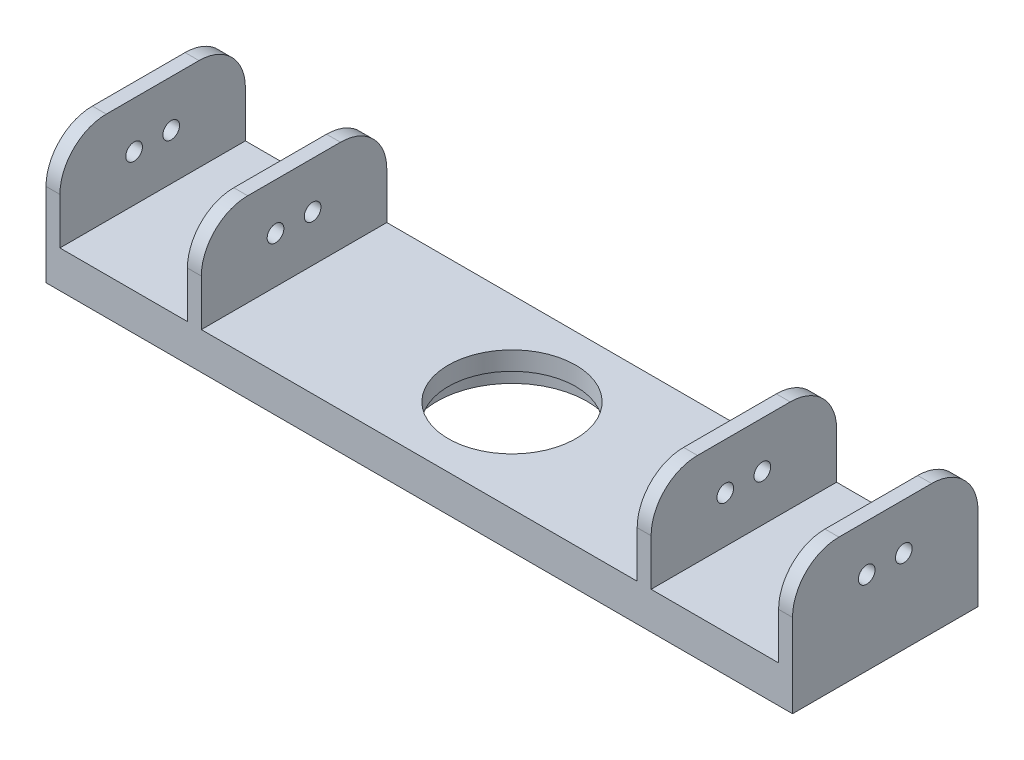
SolidWorks part; units mm, degrees
ref_plane "Front Plane" through (0, 0, 0) normal (0, 0, 1) x (1, 0, 0)
ref_plane "Top Plane" through (0, 0, 0) normal (0, 1, 0) x (1, 0, 0)
ref_plane "Right Plane" through (0, 0, 0) normal (1, 0, 0) x (0, 0, -1)
sketch "Sketch1" plane through (0, 0, 0) normal (0, 1, 0) x (1, 0, 0)
  line L0 (0, 0) -> (18.0146, 0) construction
  line L1 (18.0146, 0) -> (-21.4236, 0) construction
  line L2 (0, 0) -> (0, 10.5375) construction
  line L3 (0, 10.5375) -> (0, -15.3064) construction
  line L5 (-80.5, -20) -> (80.5, -20)
  line L6 (-80.5, -20) -> (-80.5, 20)
  line L7 (-80.5, 20) -> (80.5, 20)
  line L8 (80.5, -20) -> (80.5, 20)
  line L9 (-80.5, -20) -> (80.5, 20) construction
  line L10 (-80.5, 20) -> (80.5, -20) construction
  dimension "D1" = 40
  dimension "D2" = 161
extrude "Boss-Extrude1" add sketch "Sketch1" along normal blind 8
sketch "Sketch2" plane through (0, 8, 0) normal (0, 1, 0) x (1, 0, 0)
  line L0 (0, 0) -> (0, 39.5664) construction
  line L1 (0, 39.5664) -> (0, -35.4827) construction
  line L2 (0, 0) -> (92.9451, 0) construction
  line L3 (92.9451, 0) -> (-105.1256, 0) construction
  line L4 (80.5, 20) -> (-80.5, 20) construction
  line L5 (-50, 20) -> (-47, 20)
  line L6 (-50, 20) -> (-50, -20)
  line L7 (-50, -20) -> (-47, -20)
  line L8 (-47, 20) -> (-47, -20)
  line L9 (-80.5, -20) -> (80.5, -20) construction
  line L11 (-80.5, 20) -> (-77.5, 20)
  line L12 (-80.5, 20) -> (-80.5, -20)
  line L13 (-80.5, -20) -> (-77.5, -20)
  line L14 (-77.5, 20) -> (-77.5, -20)
  line L15 (80.5, 20) -> (77.5, 20)
  line L16 (80.5, 20) -> (80.5, -20)
  line L17 (80.5, -20) -> (77.5, -20)
  line L18 (77.5, 20) -> (77.5, -20)
  line L19 (50, 20) -> (47, 20)
  line L20 (50, 20) -> (50, -20)
  line L21 (50, -20) -> (47, -20)
  line L22 (47, 20) -> (47, -20)
  dimension "D1" = 3
  dimension "D2" = 50
  dimension "D3" = 50
extrude "Boss-Extrude2" add sketch "Sketch2" along normal blind 20
sketch "Sketch3" plane through (0, 0, 0) normal (0, -1, 0) x (1, 0, 0)
  circle A0 centre (0, 0) radius 16.2
  dimension "D1" = 32.4
extrude "Cut-Extrude1" cut sketch "Sketch3" against normal blind 4
sketch "Sketch4" plane through (-80.5, 0, 0) normal (-1, 0, 0) x (0, 0, 1)
  line L0 (0, 0) -> (0, 38.315) construction
  line L1 (-20, 0) -> (20, 0) construction
  line L2 (0, 0) -> (16.3936, 0) construction
  line L3 (0, 0) -> (-17.8484, 0) construction
  circle A0 centre (4, 18) radius 1.8
  circle A1 centre (-4, 18) radius 1.8
  dimension "D1" = 3.6
  dimension "D2" = 18
  dimension "D3" = 4
extrude "Cut-Extrude2" cut sketch "Sketch4" against normal through all both and the other way through all
sketch "Sketch5" plane through (0, 4, 0) normal (0, -1, 0) x (1, 0, 0)
  circle A0 centre (0, 0) radius 13.75
  dimension "D1" = 27.5
extrude "Cut-Extrude3" cut sketch "Sketch5" against normal up to next
fillet "Fillet1" radius 10 8 edges at (-48.5, 28, -20) (-79, 28, -20) (-79, 28, 20) (-48.5, 28, 20) (48.5, 28, -20) (48.5, 28, 20) (79, 28, 20) (79, 28, -20)
